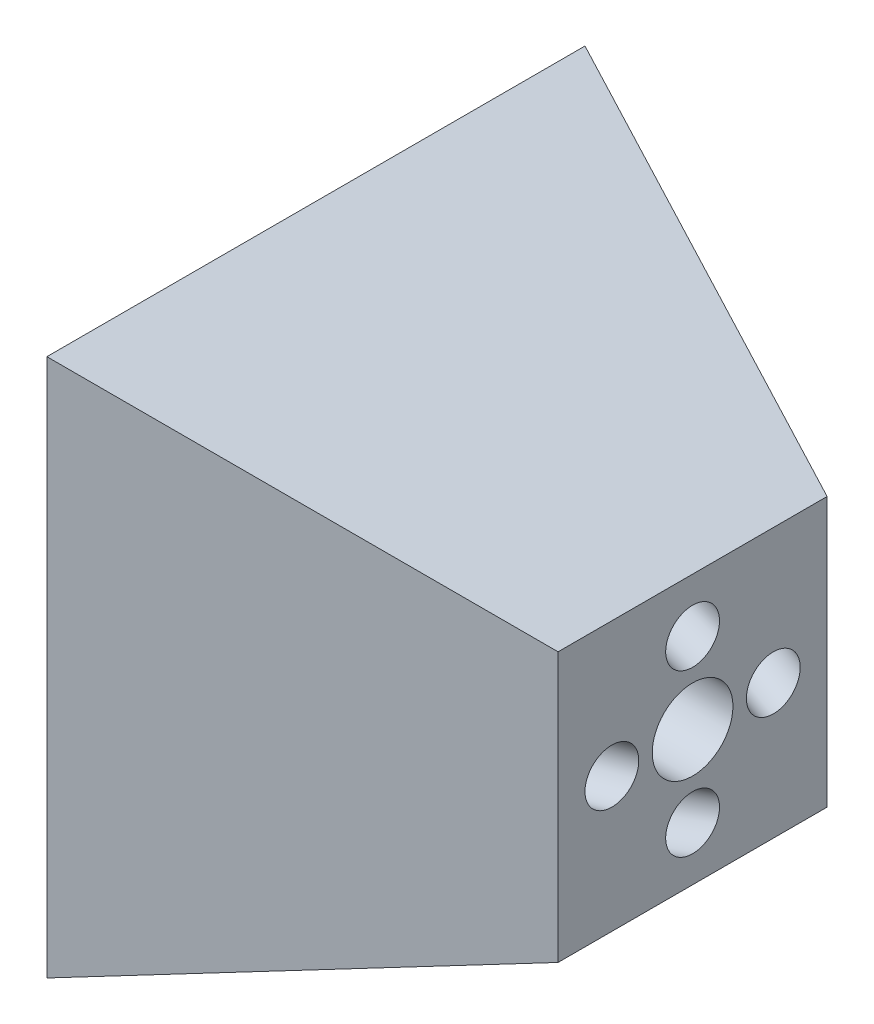
SolidWorks part; units mm, degrees
ref_plane "Front Plane" through (0, 0, 0) normal (0, 0, 1) x (1, 0, 0)
ref_plane "Top Plane" through (0, 0, 0) normal (0, 1, 0) x (1, 0, 0)
ref_plane "Right Plane" through (0, 0, 0) normal (1, 0, 0) x (0, 0, -1)
sketch "Sketch1" plane through (0, 0, 0) normal (1, 0, 0) x (0, 0, -1)
  line L1 (25, 25) -> (-25, 25)
  line L2 (25, 25) -> (25, -25)
  line L3 (25, -25) -> (-25, -25)
  line L4 (-25, 25) -> (-25, -25)
  line L5 (25, 25) -> (-25, -25) construction
  line L6 (25, -25) -> (-25, 25) construction
  point P0 (0, 0)
  dimension "D1" = 50
ref_plane "Plane1" through (-70, 0, 0) normal (1, 0, 0) x (0, 0, -1)
sketch "Sketch2" plane through (-70, 0, 0) normal (1, 0, 0) x (0, 0, -1)
  line L1 (50, 50) -> (-50, 50)
  line L2 (50, 50) -> (50, -50)
  line L3 (50, -50) -> (-50, -50)
  line L4 (-50, 50) -> (-50, -50)
  line L5 (50, 50) -> (-50, -50) construction
  line L6 (50, -50) -> (-50, 50) construction
  point P0 (0, 0)
  dimension "D1" = 100
loft "Loft1" add profiles "Sketch1", "Sketch2"
sketch "Sketch3" plane through (0, 0, 0) normal (1, 0, 0) x (0, 0, -1)
  circle A0 centre (15, 0) radius 5
  circle A1 centre (0, -15) radius 5 construction
  circle A2 centre (-15, 0) radius 5 construction
  circle A3 centre (0, 15) radius 5 construction
  point P12 (0, 0)
  dimension "D1" = 10
  dimension "D2" = 15
  dimension "D3" = 4
sketch "Sketch4" plane through (0, 0, 0) normal (0, 1, 0) x (1, 0, 0)
  line L0 (0, 15) -> (-70, 40)
  line L1 (0, 10) -> (0, 20) construction
  line L2 (-70, 50) -> (-70, -50) construction
  line L3 (0, 25) -> (-70, 50) construction
  line L5 (0, 0) -> (-133.0226, 0) construction
  line L6 (0, -15) -> (-70, -40)
sketch "Sketch5" plane through (0, 0, 0) normal (0, 0, 1) x (1, 0, 0)
  line L0 (0, 15) -> (-70, 40)
  line L1 (0, 10) -> (0, 20) construction
  line L2 (-70, 50) -> (-70, -50) construction
  line L3 (0, 25) -> (-70, 50) construction
  line L4 (0, 0) -> (34.2438, 0) construction
  line L5 (0, -15) -> (-70, -40)
sweep "Cut-Sweep2" cut profiles "Sketch3" path "Sketch4"
sketch "Sketch6" plane through (0, 0, 0) normal (1, 0, 0) x (0, 0, -1)
  circle A0 centre (0, 15) radius 5 construction
  circle A1 centre (15, 0) radius 5
  circle A2 centre (15, 0) radius 5 construction
  circle A3 centre (0, 15) radius 5
  dimension "D1" = 0
sweep "Cut-Sweep3" cut profiles "Sketch6" path "Sketch5"
mirror "Mirror1" about plane through (0, 0, 0) normal (0, 0, 1) of "Cut-Sweep2"
mirror "Mirror2" about plane through (0, 0, 0) normal (0, 1, 0) of "Cut-Sweep3"
sketch "Sketch7" plane through (0, 0, 0) normal (1, 0, 0) x (0, 0, -1)
  circle A0 centre (0, 0) radius 7.5
  dimension "D1" = 15
extrude "Cut-Extrude1" cut sketch "Sketch7" against normal through all
